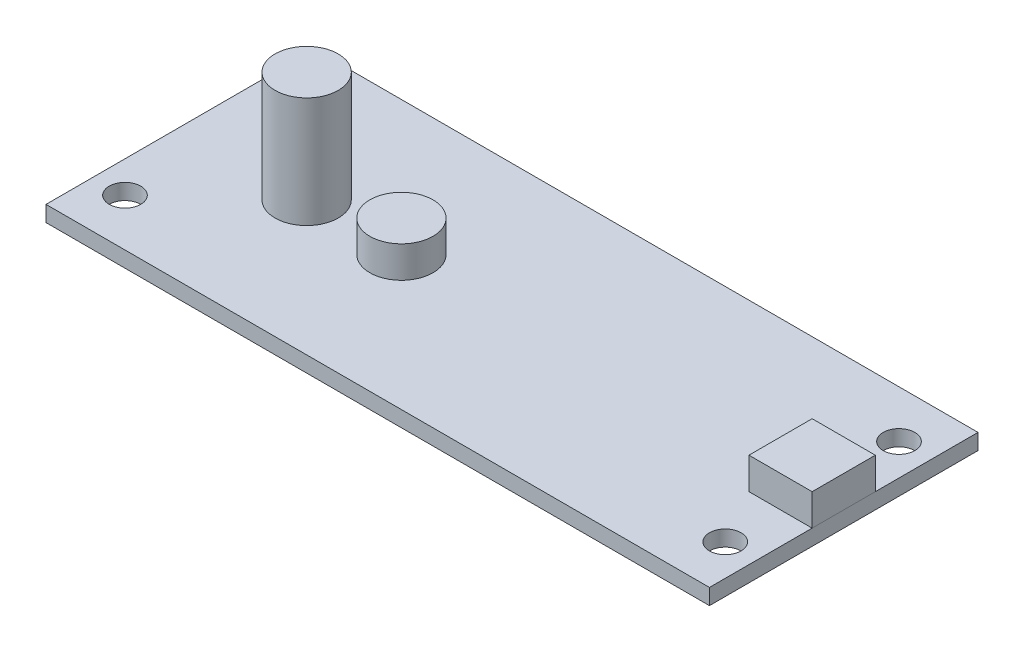
SolidWorks part; units mm, degrees
ref_plane "Front Plane" through (0, 0, 0) normal (0, 0, 1) x (1, 0, 0)
ref_plane "Top Plane" through (0, 0, 0) normal (0, 1, 0) x (1, 0, 0)
ref_plane "Right Plane" through (0, 0, 0) normal (1, 0, 0) x (0, 0, -1)
sketch "Sketch1" plane through (0, 0, 0) normal (0, 1, 0) x (1, 0, 0)
  line L1 (-33.3375, 13.4938) -> (33.3375, 13.4938)
  line L2 (-33.3375, 13.4938) -> (-33.3375, -13.4937)
  line L3 (-33.3375, -13.4937) -> (33.3375, -13.4937)
  line L4 (33.3375, 13.4938) -> (33.3375, -13.4937)
  line L5 (-33.3375, 13.4938) -> (33.3375, -13.4937) construction
  line L6 (-33.3375, -13.4937) -> (33.3375, 13.4938) construction
  point P0 (0, 0)
  dimension "D1" = 66.675
  dimension "D2" = 26.9875
extrude "Boss-Extrude1" add sketch "Sketch1" along normal blind 1.5875
sketch "Sketch2" plane through (0, 1.5875, 0) normal (0, 1, 0) x (1, 0, 0)
  line L0 (33.3375, 13.4938) -> (-33.3375, 13.4938) construction
  line L1 (-25.4, 13.4938) -> (25.4, 13.4938)
  line L2 (-25.4, 13.4938) -> (-25.4, 11.1125)
  line L3 (-25.4, 11.1125) -> (25.4, 11.1125)
  line L4 (25.4, 13.4938) -> (25.4, 11.1125)
  line L5 (-33.3375, -13.4937) -> (33.3375, -13.4937) construction
  line L6 (-25.4, -13.4937) -> (25.4, -13.4937)
  line L7 (-25.4, -13.4937) -> (-25.4, -11.1125)
  line L8 (-25.4, -11.1125) -> (25.4, -11.1125)
  line L9 (25.4, -13.4937) -> (25.4, -11.1125)
  line L10 (-33.3375, 13.4938) -> (-33.3375, -13.4937) construction
  circle A0 centre (-20.6375, 0) radius 3.175
  point P12 (0, 11.1125)
  point P13 (0, -11.1125)
  dimension "D4" = 6.35
  dimension "D1" = 2.3813
  dimension "D2" = 50.8
  dimension "D3" = 12.7
extrude "Boss-Extrude2" add sketch "Sketch2" along normal blind 11.1125 separate body contours A0
sketch "Sketch3" plane through (0, 1.5875, 0) normal (0, 1, 0) x (1, 0, 0)
  line L0 (33.3375, -13.4937) -> (33.3375, 13.4938) construction
  line L1 (33.3375, 3.175) -> (26.9875, 3.175)
  line L2 (33.3375, 3.175) -> (33.3375, -3.175)
  line L3 (33.3375, -3.175) -> (26.9875, -3.175)
  line L4 (26.9875, 3.175) -> (26.9875, -3.175)
  circle A0 centre (-11.1125, 0) radius 3.175
  circle A2 centre (-20.6375, 0) radius 3.175 construction
  point P6 (26.9875, 0)
  dimension "D3" = 6.35
  dimension "D4" = 9.525
  dimension "D1" = 6.35
  dimension "D2" = 6.35
extrude "Boss-Extrude3" add sketch "Sketch3" along normal blind 3.175 separate body
sketch "Sketch4" plane through (0, 1.5875, 0) normal (0, 1, 0) x (1, 0, 0)
  line L0 (-33.3375, -13.4937) -> (33.3375, -13.4937) construction
  line L1 (-33.3375, 13.4938) -> (-33.3375, -13.4937) construction
  line L2 (33.3375, 13.4938) -> (-33.3375, 13.4938) construction
  line L3 (33.3375, -13.4937) -> (33.3375, 13.4938) construction
  circle A0 centre (30.1625, -8.7312) radius 1.5875
  circle A1 centre (30.1625, 8.7313) radius 1.5875
  circle A2 centre (-30.1625, 8.7313) radius 1.5875
  circle A3 centre (-30.1625, -8.7312) radius 1.5875
  dimension "D5" = 3.175
  dimension "D1" = 4.7625
  dimension "D2" = 3.175
  dimension "D3" = 4.7625
  dimension "D4" = 3.175
extrude "Cut-Extrude1" cut sketch "Sketch4" against normal through all
